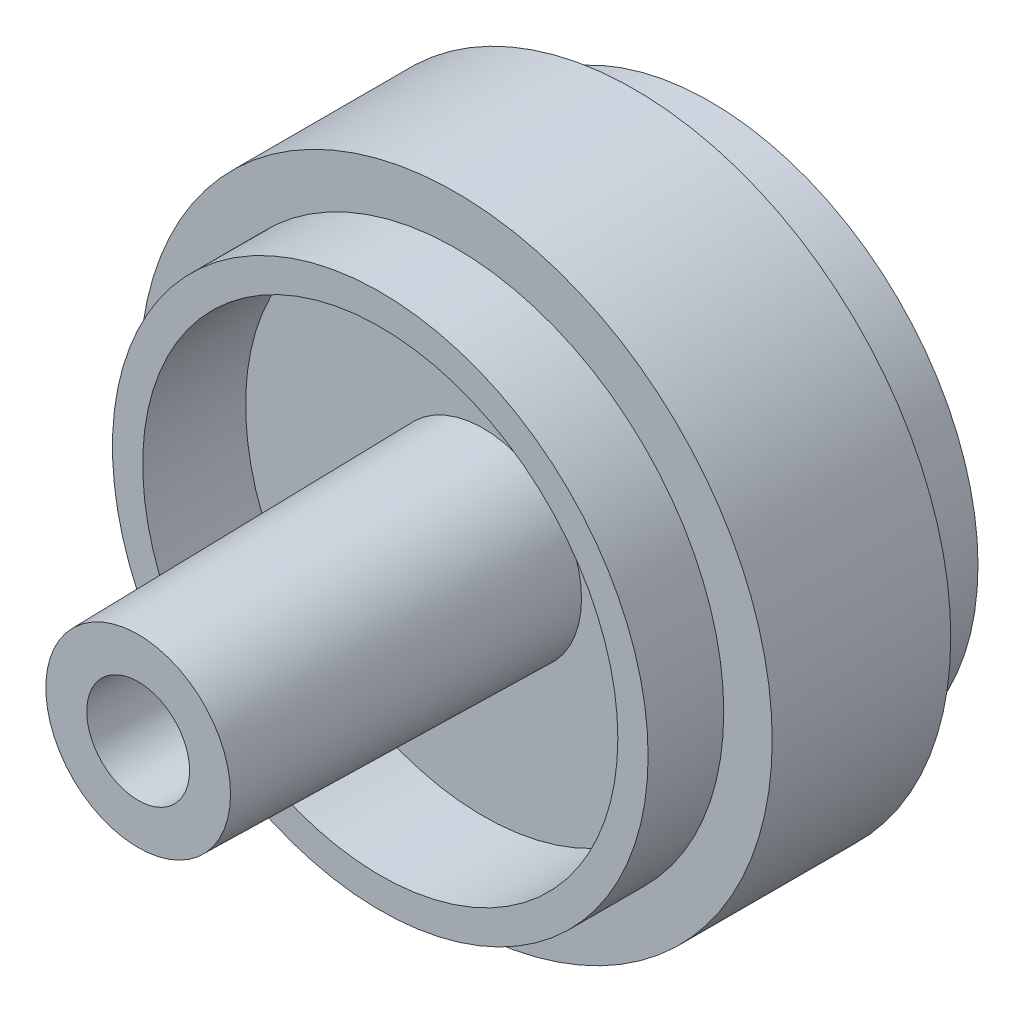
SolidWorks part; units mm, degrees
ref_plane "Front Plane" through (0, 0, 0) normal (0, 0, 1) x (1, 0, 0)
ref_plane "Top Plane" through (0, 0, 0) normal (0, 1, 0) x (1, 0, 0)
ref_plane "Right Plane" through (0, 0, 0) normal (1, 0, 0) x (0, 0, -1)
sketch "Sketch2" plane through (0, 0, 0) normal (1, 0, 0) x (0, 0, -1)
  line L0 (-8.8339, 0) -> (10.9059, 0) construction
  line L1 (-2.05, 3.25) -> (5.45, 3.25)
  line L2 (5.45, 3.25) -> (5.45, 4.25)
  line L3 (5.45, 4.25) -> (2.05, 4.25)
  line L4 (2.05, 4.25) -> (2.05, 7.85)
  line L5 (2.05, 7.85) -> (5.45, 7.85)
  line L6 (5.45, 7.85) -> (5.45, 8.85)
  line L7 (5.45, 8.85) -> (2.95, 8.85)
  line L8 (2.95, 8.85) -> (2.95, 10.45)
  line L9 (2.95, 10.45) -> (-2.95, 10.45)
  line L10 (-2.95, 8.85) -> (-2.95, 10.45)
  line L11 (0, -5.1804) -> (0, 14.5978) construction
  line L12 (-5.45, 8.85) -> (-2.95, 8.85)
  line L13 (-5.45, 7.85) -> (-5.45, 8.85)
  line L14 (-2.05, 7.85) -> (-5.45, 7.85)
  line L15 (-2.05, 3.25) -> (-2.05, 7.85)
  point P16 (0, 10.45)
  point P23 (0, 3.25)
  dimension "D1" = 5.45
  dimension "D2" = 3.25
  dimension "D3" = 1
  dimension "D4" = 1
  dimension "D5" = 3.4
  dimension "D6" = 2.5
  dimension "D7" = 1.6
  dimension "D8" = 3.6
revolve "Revolve2" add sketch "Sketch2" angle 360 about L0
sketch "Sketch3" plane through (0, 0, 2.05) normal (0, 0, 1) x (1, 0, 0)
  circle A0 centre (0, 0) radius 3.25
  circle A1 centre (0, 0) radius 1.5
  dimension "D1" = 3
extrude "Boss-Extrude2" add sketch "Sketch3" along normal blind 11.4 draft 1 and the other way blind 1
